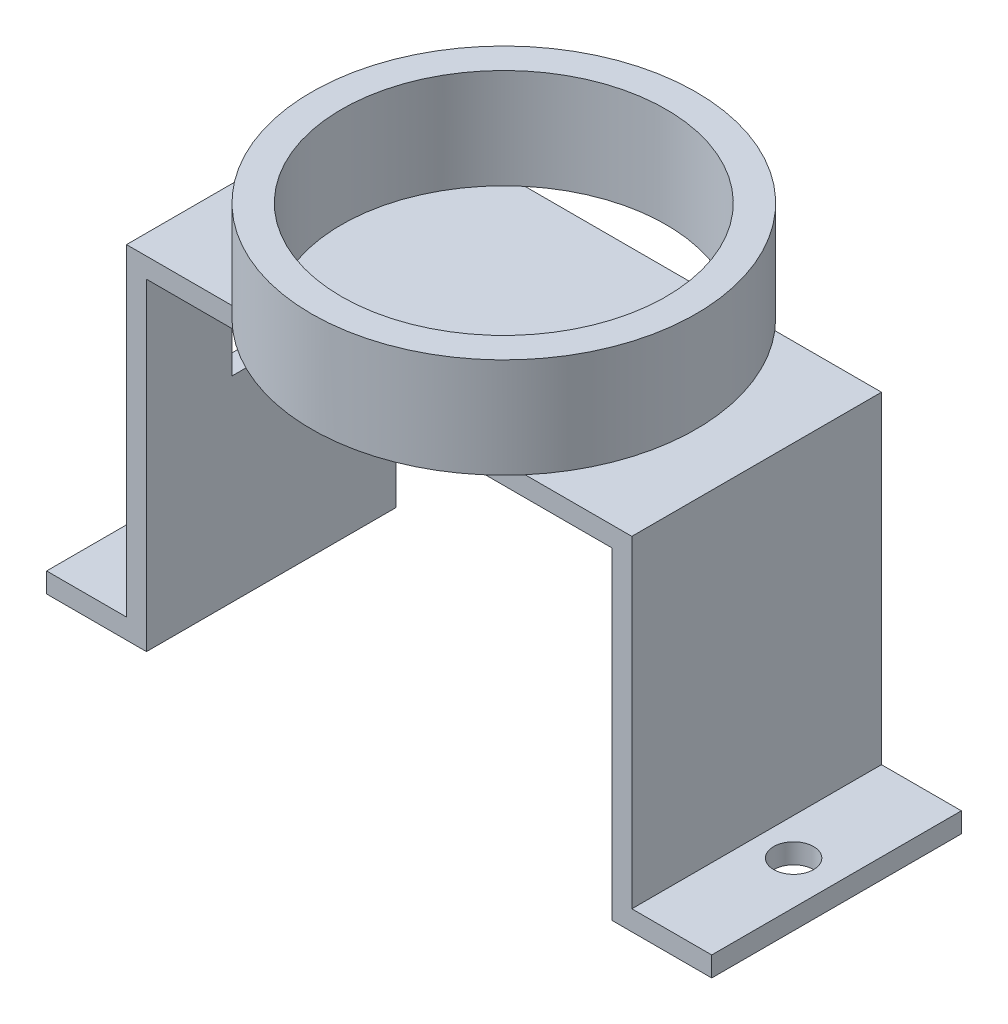
SolidWorks part; units mm, degrees
ref_plane "Ön Düzlem" through (0, 0, 0) normal (0, 0, 1) x (1, 0, 0)
ref_plane "Üst Düzlem" through (0, 0, 0) normal (0, 1, 0) x (1, 0, 0)
ref_plane "Sağ Düzlem" through (0, 0, 0) normal (1, 0, 0) x (0, 0, -1)
sketch "Çizim1" plane through (0, 0, 0) normal (0, 0, 1) x (1, 0, 0)
  line L0 (0, 0) -> (-5, 0)
  line L2 (0, 0) -> (0, 16.15)
  line L3 (0, 16.15) -> (23.3, 16.15)
  line L4 (23.3, 0) -> (23.3, 16.15)
  line L5 (23.3, 0) -> (28.3, 0)
  dimension "D1" = 23.3
  dimension "D2" = 16.15
  dimension "D3" = 5
extrude "Ekstrüzyon-İnce1" add sketch "Çizim1" along normal blind 12.5 thin
sketch "Çizim2" plane through (0, 1, 0) normal (0, 1, 0) x (1, 0, 0)
  circle A0 centre (-2.85, -6.25) radius 1 construction
  circle A1 centre (-2.85, -6.25) radius 1
  circle A2 centre (26.15, -6.25) radius 1 construction
  circle A3 centre (26.15, -6.25) radius 1
extrude "Kes-Ekstrüzyon1" cut sketch "Çizim2" against normal through all
sketch "Çizim3" plane through (-1, 0, 0) normal (-1, 0, 0) x (0, 0, 1)
  line L1 (4.2558, 9.8136) -> (8.2252, 9.8136)
  line L2 (4.2558, 9.8136) -> (4.2558, 11.8368)
  line L3 (4.2558, 11.8368) -> (8.2252, 11.8368)
  line L4 (8.2252, 9.8136) -> (8.2252, 11.8368)
extrude "Kes-Ekstrüzyon2" cut sketch "Çizim3" against normal blind 3
sketch "Çizim4" plane through (0, 17.15, 0) normal (0, 1, 0) x (1, 0, 0)
  circle A0 centre (11.64, -6.25) radius 8.125
  circle A1 centre (11.64, -6.25) radius 9.625
  dimension "D1" = 16.25
  dimension "D2" = 1.5
extrude "Yükseklik-Ekstrüzyon1" add sketch "Çizim4" along normal blind 5
